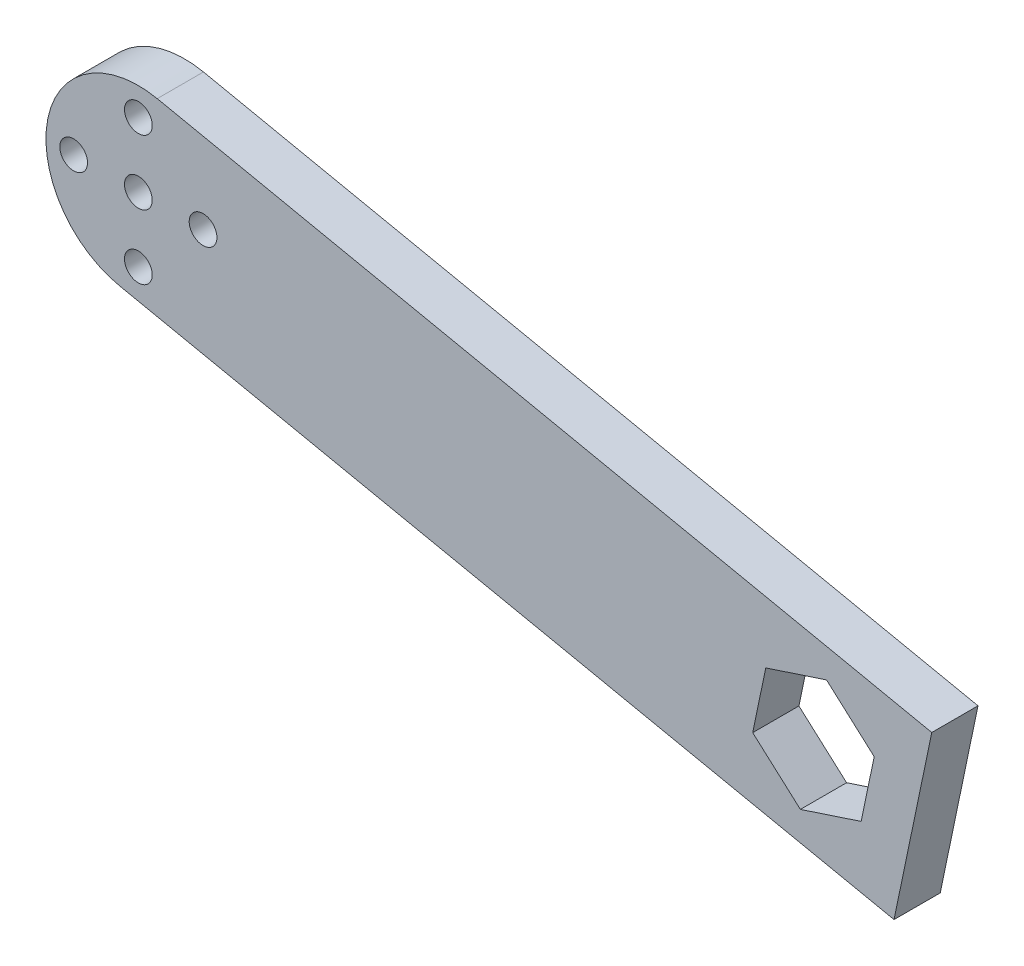
SolidWorks part; units mm, degrees
ref_plane "Front Plane" through (0, 0, 0) normal (0, 0, 1) x (1, 0, 0)
ref_plane "Top Plane" through (0, 0, 0) normal (0, 1, 0) x (1, 0, 0)
ref_plane "Right Plane" through (0, 0, 0) normal (1, 0, 0) x (0, 0, -1)
sketch "Sketch2" plane through (0, 0, 0) normal (0, 0, 1) x (1, 0, 0)
  line L0 (2.043, 9.7891) -> (85.8466, -7.7009)
  line L1 (-2.043, -9.7891) -> (81.7606, -27.2791)
  line L2 (85.8466, -7.7009) -> (81.7606, -27.2791)
  line L4 (83.8036, -17.49) -> (0, 0) construction
  line L5 (74.4563, -8.4701) -> (67.8829, -10.6328)
  line L6 (67.8829, -10.6328) -> (66.4691, -17.4068)
  line L7 (66.4691, -17.4068) -> (71.6288, -22.0182)
  line L8 (71.6288, -22.0182) -> (78.2021, -19.8555)
  line L9 (78.2021, -19.8555) -> (79.6159, -13.0815)
  line L10 (79.6159, -13.0815) -> (74.4563, -8.4701)
  circle A1 centre (0, 0) radius 1.5
  circle A2 centre (0, 7) radius 1.5
  circle A3 centre (0, -7) radius 1.5
  circle A4 centre (7, 0) radius 1.5
  circle A5 centre (-7, 0) radius 1.5
  arc A6 (2.043, 9.7891) -> (-2.043, -9.7891) centre (0, 0) ccw
  circle A7 centre (73.0425, -15.2441) radius 5.9929 construction
  point P26 (78.909, -16.4685)
  dimension "D1" = 3
  dimension "D2" = 3
  dimension "D3" = 3
  dimension "D4" = 3
  dimension "D5" = 3
  dimension "D6" = 20
  dimension "D7" = 6.92
  dimension "D8" = 5
extrude "Boss-Extrude1" add sketch "Sketch2" along normal blind 5
